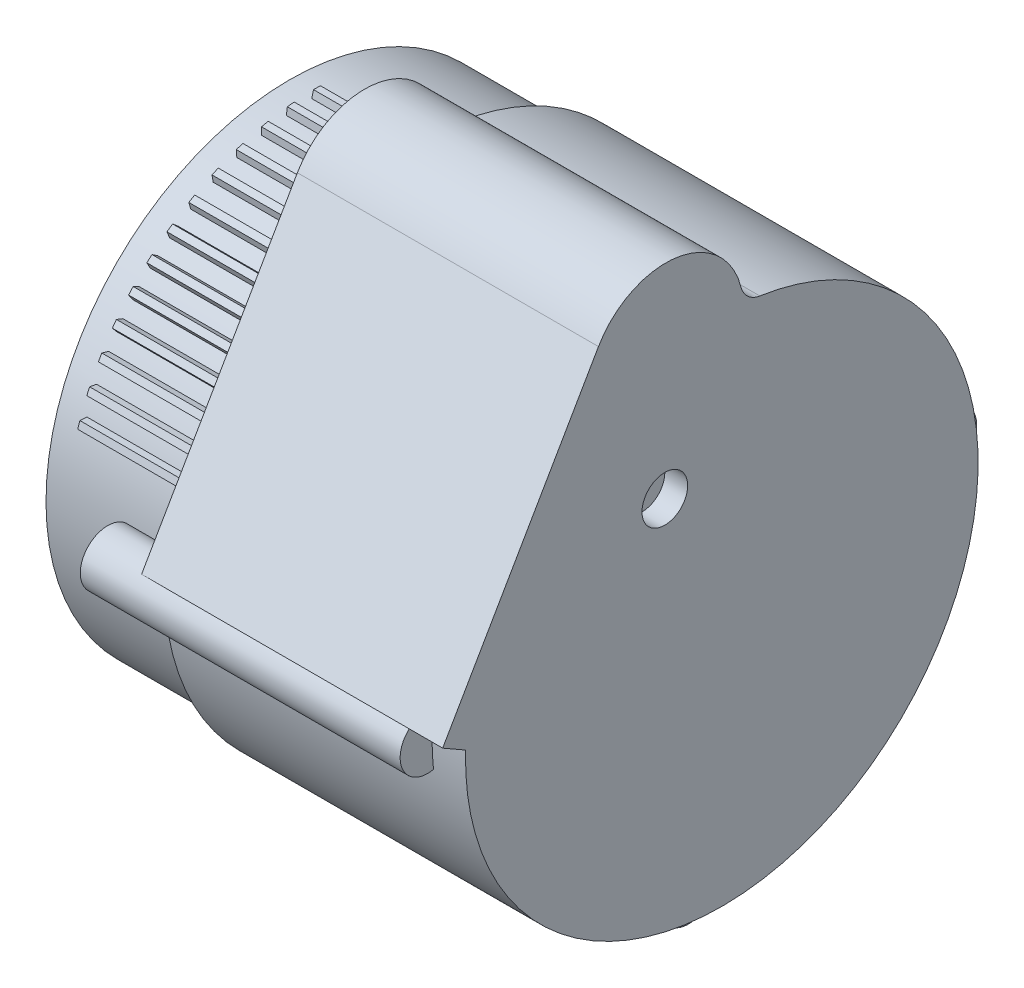
SolidWorks part; units mm, degrees
ref_plane "Front Plane" through (0, 0, 0) normal (0, 0, 1) x (1, 0, 0)
ref_plane "Top Plane" through (0, 0, 0) normal (0, 1, 0) x (1, 0, 0)
ref_plane "Right Plane" through (0, 0, 0) normal (1, 0, 0) x (0, 0, -1)
sketch "Sketch2" plane through (0, 0, 0) normal (1, 0, 0) x (0, 0, -1)
  circle A0 centre (0, 0) radius 53.3
  dimension "D1" = 106.6
extrude "Boss-Extrude1" add sketch "Sketch2" along normal blind 94.62
ref_plane "Plane1" through (6, 0, 0) normal (-1, 0, 0) x (0, 0, 1)
sketch "Sketch4" plane through (6, 0, 0) normal (-1, 0, 0) x (0, 0, 1)
  line L0 (0, 53.3) -> (0, 54.8) construction
  line L1 (-0.75, 54.8) -> (0.75, 54.8)
  line L2 (-0.75, 54.8) -> (-1.125, 53.2881)
  line L3 (0.75, 54.8) -> (1.125, 53.2881)
  line L4 (-1.125, 53.2881) -> (1.125, 53.2881)
  circle A0 centre (0, 0) radius 53.3 construction
  point P8 (0, 54.8)
  dimension "D1" = 1.5
  dimension "D2" = 2.25
  dimension "D3" = 1.5
extrude "Boss-Extrude2" add sketch "Sketch4" against normal blind 83
pattern_circular "CirPattern1" count 13 every 6 about axis through (0, 0, 0) along (1, 0, 0) of "Boss-Extrude2"
ref_plane "Plane2" through (47.31, 0, 0) normal (-1, 0, 0) x (0, 0, 1)
sketch "Sketch5" plane through (47.31, 0, 0) normal (-1, 0, 0) x (0, 0, 1)
  line L0 (-53.3, 0) -> (-63.1, 0)
  circle A0 centre (0, 0) radius 63.1 construction
  circle A1 centre (0, 0) radius 53.3 construction
  circle A2 centre (-57.1, 0) radius 6
  dimension "D1" = 126.2
  dimension "D2" = 12
extrude "Boss-Extrude3" add sketch "Sketch5" along normal blind 30 and the other way blind 40
pattern_circular "CirPattern2" count 3 every 90 about axis through (0, 0, 0) along (1, 0, 0) of "Boss-Extrude3"
sketch "Sketch6" plane through (94.62, 0, 0) normal (1, 0, 0) x (0, 0, -1)
  line L0 (-61.1, 4.4721) -> (-27, 63.5351)
  line L1 (63.1, 0) -> (56.1, 0) construction
  line L2 (-61.1, 4.4721) -> (-56.0774, 1.5924)
  line L3 (-56.1, 0) -> (-63.1, 0) construction
  arc A0 (-53.1112, 4.4821) -> (-53.1112, -4.4821) centre (-57.1, 0) ccw construction
  arc A1 (53.1112, -4.4821) -> (53.1112, 4.4821) centre (57.1, 0) ccw construction
  arc A6 (-27, 63.5351) -> (4.7003, 55.9027) centre (-12.2776, 55.0351) cw
  circle A7 centre (0, 0) radius 53.3 construction
  arc A9 (-56.0774, 1.5924) -> (4.7003, 55.9027) centre (0, 0) ccw
  circle A10 centre (0, 0) radius 53.3
  dimension "D2" = 2
  dimension "D3" = 68.2
  dimension "D4" = 2.8
  dimension "D5" = 17
  dimension "D6" = 5.7896
  dimension "D1" = 60
extrude "Boss-Extrude4" add sketch "Sketch6" against normal blind 65.9
fillet "Fillet2" radius 5 1 edges at (61.67, 55.9027, -4.7003)
sketch "Sketch7" plane through (94.62, 0, 0) normal (1, 0, 0) x (0, 0, -1)
  line L0 (-61.1, 4.4721) -> (-64.5406, 6.4586) construction
  line L3 (-47.85, 27.4218) -> (-40.9218, 23.4218) construction
  line L4 (-27, 63.5351) -> (-61.1, 4.4721) construction
  circle A0 centre (0, 0) radius 14 construction
  circle A1 centre (-12.4751, 27.4218) radius 28.7265 construction
  circle A2 centre (-12.4751, 27.4218) radius 5
  dimension "D2" = 28
  dimension "D4" = 57.453
  dimension "D5" = 10
  dimension "D1" = 26.5
  dimension "D3" = 8
extrude "Cut-Extrude1" cut sketch "Sketch7" against normal blind 5
